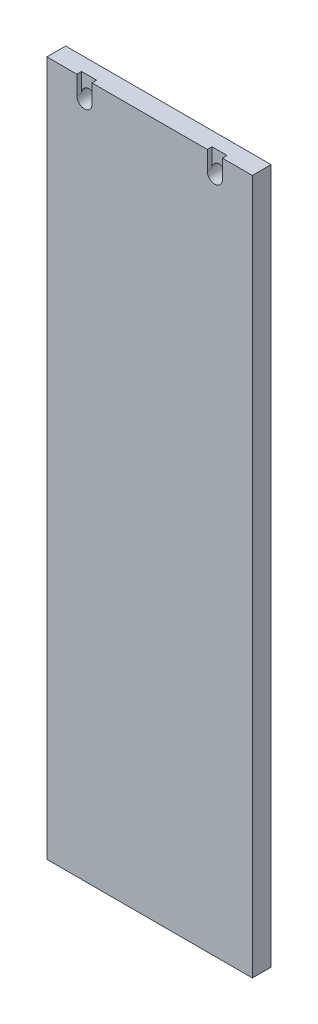
SolidWorks part; units mm, degrees
material "PVC Rigid"
ref_plane "Front" through (0, 0, 0) normal (0, 0, 1) x (1, 0, 0)
ref_plane "Top" through (0, 0, 0) normal (0, 1, 0) x (1, 0, 0)
ref_plane "Right" through (0, 0, 0) normal (1, 0, 0) x (0, 0, -1)
sketch "Sketch1" plane through (0, 0, 0) normal (0, 0, 1) x (1, 0, 0)
  line L0 (69.5, -206.525) -> (72.675, -206.525) construction
  line L1 (0, 15.875) -> (69.5, 15.875) construction
  line L2 (0, 15.875) -> (0, -206.525)
  line L3 (0, -206.525) -> (69.5, -206.525)
  line L4 (69.5, 15.875) -> (69.5, -206.525)
  line L5 (69.5, -206.525) -> (69.5, 15.875) construction
  line L6 (0, 15.875) -> (0, 28.575)
  line L7 (0, 28.575) -> (69.5, 28.575)
  line L8 (69.5, 28.575) -> (69.5, 15.875)
  dimension "D1" = 12.7
extrude "Boss-Extrude1" add sketch "Sketch1" against normal blind 6.35
sketch "String Hole Pattern" plane through (0, 0, 0) normal (0, 0, 1) x (1, 0, 0)
  line L1 (34.75, 28.575) -> (34.75, 10.2008) construction
  line L6 (0, 15.875) -> (0, -206.525)
  line L7 (0, -206.525) -> (69.5, -206.525)
  line L8 (69.5, -206.525) -> (69.5, 15.875)
  line L9 (69.5, 15.875) -> (69.5, 28.575)
  line L10 (69.5, 28.575) -> (0, 28.575)
  line L11 (0, 28.575) -> (0, 15.875)
  line L12 (0, 15.875) -> (0, -206.525)
  line L13 (0, -206.525) -> (69.5, -206.525)
  line L14 (69.5, -206.525) -> (69.5, 15.875)
  line L15 (69.5, 15.875) -> (69.5, 28.575)
  line L16 (69.5, 28.575) -> (0, 28.575)
  line L17 (0, 28.575) -> (0, 15.875)
  point P5 (12.7, 22.225)
  point P9 (0, 22.225)
  point P13 (56.8, 22.225)
  dimension "D2" = 12.7
  dimension "D1" = 0
hole_wizard "#10 Clearance Hole1" positions "Sketch3" profile "Sketch4" hole size "#10" standard "ANSI Inch" end condition through all
sketch "Sketch3" plane through (0, 0, 0) normal (0, 0, 1) x (1, 0, 0)
  point P0 (12.7, 22.225)
  point P3 (56.8, 22.225)
sketch "Sketch4" plane through (12.7, 22.225, 0) normal (1, 0, 0) x (0, -1, 0)
  line L0 (0, 0) -> (0, 6.35)
  line L1 (0, 6.35) -> (2.5527, 6.35)
  line L2 (2.5527, 6.35) -> (2.5527, 0)
  line L5 (2.5527, 0) -> (0, 0)
  line L11 (0, -6.35) -> (0, 107.95) construction
  dimension "Thru Hole Dia." = 5.1054
  dimension "Thru Hole Depth" = 6.35
sketch "Sketch6" plane through (0, 0, 0) normal (0, 0, -1) x (-1, 0, 0)
  line L0 (-69.5, 28.575) -> (0, 28.575) construction
  line L1 (-69.5, 28.575) -> (0, 28.575) construction
  line L2 (-59.3527, 22.225) -> (-59.3527, 28.575)
  line L3 (-59.3527, 28.575) -> (-54.2473, 28.575)
  line L4 (-54.2473, 28.575) -> (-54.2473, 22.225)
  line L5 (-34.75, 28.575) -> (-34.75, 10.2008) construction
  line L6 (-34.75, 28.575) -> (-34.75, 10.2008) construction
  line L7 (-10.1473, 22.225) -> (-10.1473, 28.575)
  line L8 (-10.1473, 28.575) -> (-15.2527, 28.575)
  line L9 (-15.2527, 28.575) -> (-15.2527, 22.225)
  circle A0 centre (-56.8, 22.225) radius 2.5527 construction
  circle A1 centre (-56.8, 22.225) radius 2.5527 construction
  arc A2 (-59.3527, 22.225) -> (-54.2473, 22.225) centre (-56.8, 22.225) ccw
  arc A3 (-10.1473, 22.225) -> (-15.2527, 22.225) centre (-12.7, 22.225) cw
extrude "Cut-Extrude1" cut sketch "Sketch6" along normal blind 1.5875
equation "\"D1@Sketch1\"=\"acc side wall extra height@FS2-EN-ACC-A-0001-V1, FULL ACCUMULATOR ASSEMBLY.Assembly\""
